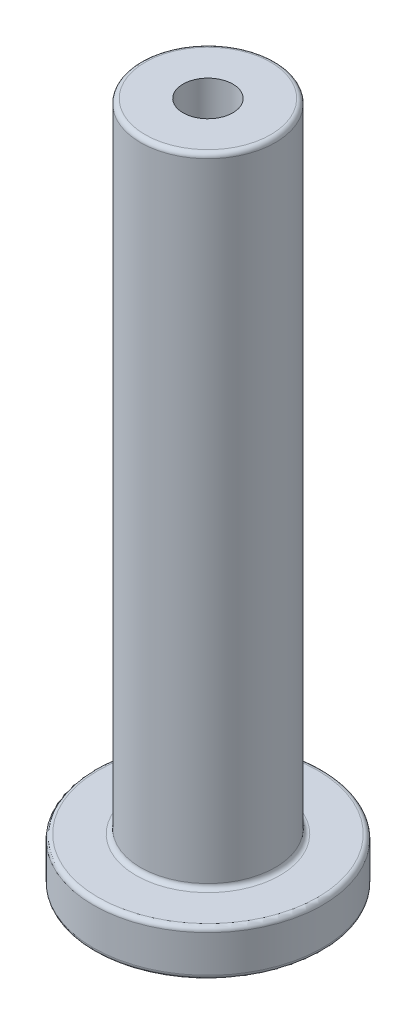
SolidWorks part; units mm, degrees
ref_plane "Front Plane" through (0, 0, 0) normal (0, 0, 1) x (1, 0, 0)
ref_plane "Top Plane" through (0, 0, 0) normal (0, 1, 0) x (1, 0, 0)
ref_plane "Right Plane" through (0, 0, 0) normal (1, 0, 0) x (0, 0, -1)
sketch "Sketch1" plane through (0, 0, 0) normal (0, 1, 0) x (1, 0, 0)
  circle A0 centre (0, 0) radius 12.4
  dimension "D1" = 24.8
extrude "Boss-Extrude1" add sketch "Sketch1" along normal blind 5
sketch "Sketch2" plane through (0, 5, 0) normal (0, 1, 0) x (1, 0, 0)
  circle A0 centre (0, 0) radius 7.3
  dimension "D1" = 14.6
extrude "Boss-Extrude2" add sketch "Sketch2" along normal blind 69
sketch "Sketch3" plane through (0, 74, 0) normal (0, 1, 0) x (1, 0, 0)
  circle A0 centre (0, 0) radius 2.7
  dimension "D1" = 5.4
extrude "Cut-Extrude1" cut sketch "Sketch3" against normal through all
sketch "Sketch4" plane through (0, 0, 0) normal (0, -1, 0) x (1, 0, 0)
  line L1 (-4.3802, 2.0818) -> (-3.993, -2.7525)
  line L2 (-3.993, -2.7525) -> (0.3872, -4.8343)
  line L3 (0.3872, -4.8343) -> (4.3802, -2.0818)
  line L4 (4.3802, -2.0818) -> (3.993, 2.7525)
  line L5 (3.993, 2.7525) -> (-0.3872, 4.8343)
  line L6 (-0.3872, 4.8343) -> (-4.3802, 2.0818)
  circle A0 centre (0, 0) radius 4.2 construction
  dimension "D1" = 8.4
extrude "Cut-Extrude2" cut sketch "Sketch4" against normal blind 3
fillet "Fillet1" radius 0.5 4 edges at (0, 0, 12.4) (0, 5, 12.4) (0, 74, 7.3) (0, 5, 7.3)
